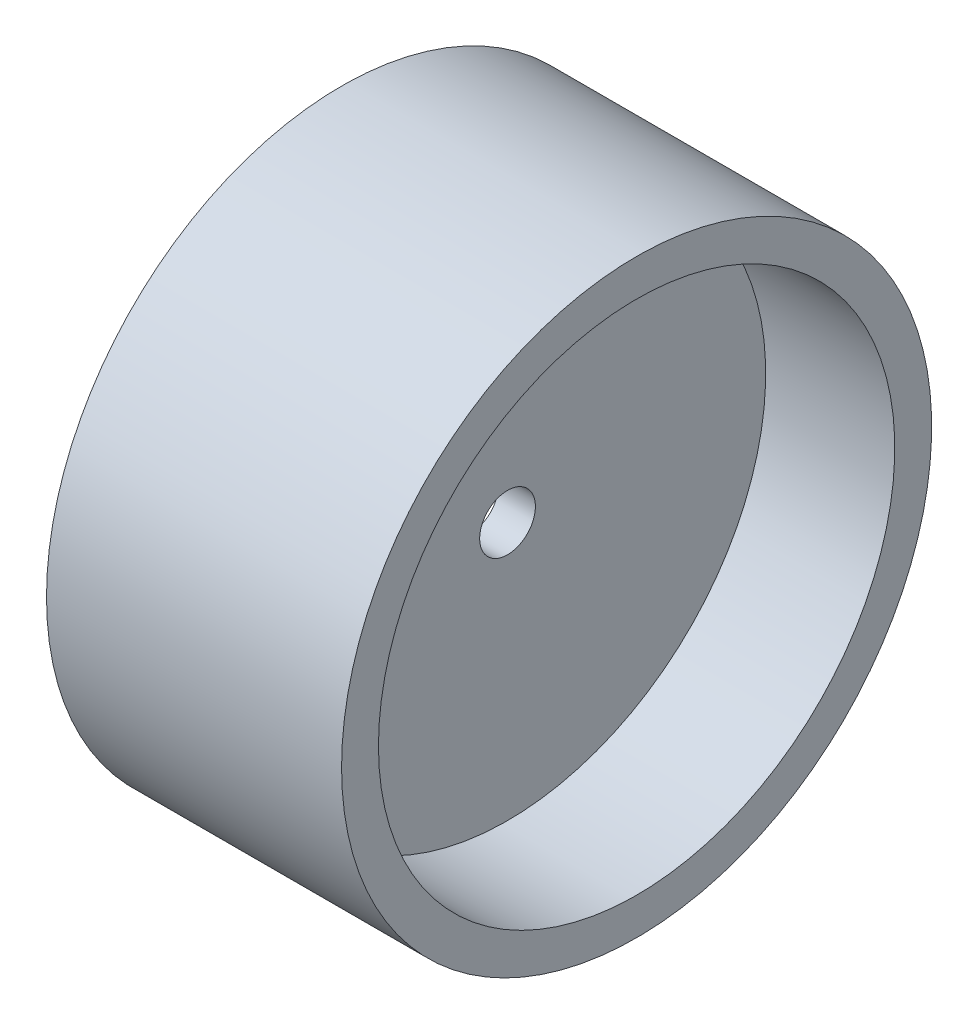
SolidWorks part; units mm, degrees
ref_plane "Front Plane" through (0, 0, 0) normal (0, 0, 1) x (1, 0, 0)
ref_plane "Top Plane" through (0, 0, 0) normal (0, 1, 0) x (1, 0, 0)
ref_plane "Right Plane" through (0, 0, 0) normal (1, 0, 0) x (0, 0, -1)
sketch "Sketch1" plane through (0, 0, 0) normal (0, 0, 1) x (1, 0, 0)
  line L0 (0, 0) -> (25.4, 0) construction
  line L1 (0, 0) -> (0, 25.4)
  line L3 (-12.7, 22.225) -> (12.7, 22.225)
  line L4 (-12.7, 22.225) -> (-12.7, 25.4)
  line L5 (-12.7, 25.4) -> (12.7, 25.4)
  line L6 (12.7, 22.225) -> (12.7, 25.4)
  line L7 (-12.7, 22.225) -> (12.7, 25.4) construction
  line L8 (-12.7, 25.4) -> (12.7, 22.225) construction
  line L9 (1.5875, 0) -> (-1.5875, 0)
  line L10 (1.5875, 0) -> (1.5875, 22.225)
  line L11 (1.5875, 22.225) -> (-1.5875, 22.225)
  line L12 (-1.5875, 0) -> (-1.5875, 22.225)
  line L13 (1.5875, 0) -> (-1.5875, 22.225) construction
  line L14 (1.5875, 22.225) -> (-1.5875, 0) construction
  point P3 (0, 23.8125)
  point P9 (0, 11.1125)
  dimension "D1" = 25.4
  dimension "D2" = 25.4
  dimension "D3" = 25.4
  dimension "D4" = 3.175
  dimension "D5" = 3.175
revolve "Revolve1" add sketch "Sketch1" angle 360 about L0
hole_wizard "M4 Clearance Hole1" positions "Sketch2" profile "Sketch3" hole size "M4" standard "ANSI Metric" end condition through all
sketch "Sketch2" plane through (-1.5875, 0, 0) normal (-1, 0, 0) x (0, 0, 1)
  point P0 (0, 0)
sketch "Sketch3" plane through (-1.5875, 0, 0) normal (0, 1, 0) x (0, 0, 1)
  line L0 (0, 0) -> (0, 14.2875)
  line L1 (0, 14.2875) -> (2.4, 14.2875)
  line L2 (2.4, 14.2875) -> (2.4, 0)
  line L5 (2.4, 0) -> (0, 0)
  line L11 (0, -6.35) -> (0, 107.95) construction
  dimension "Thru Hole Dia." = 4.8
  dimension "Thru Hole Depth" = 14.2875
